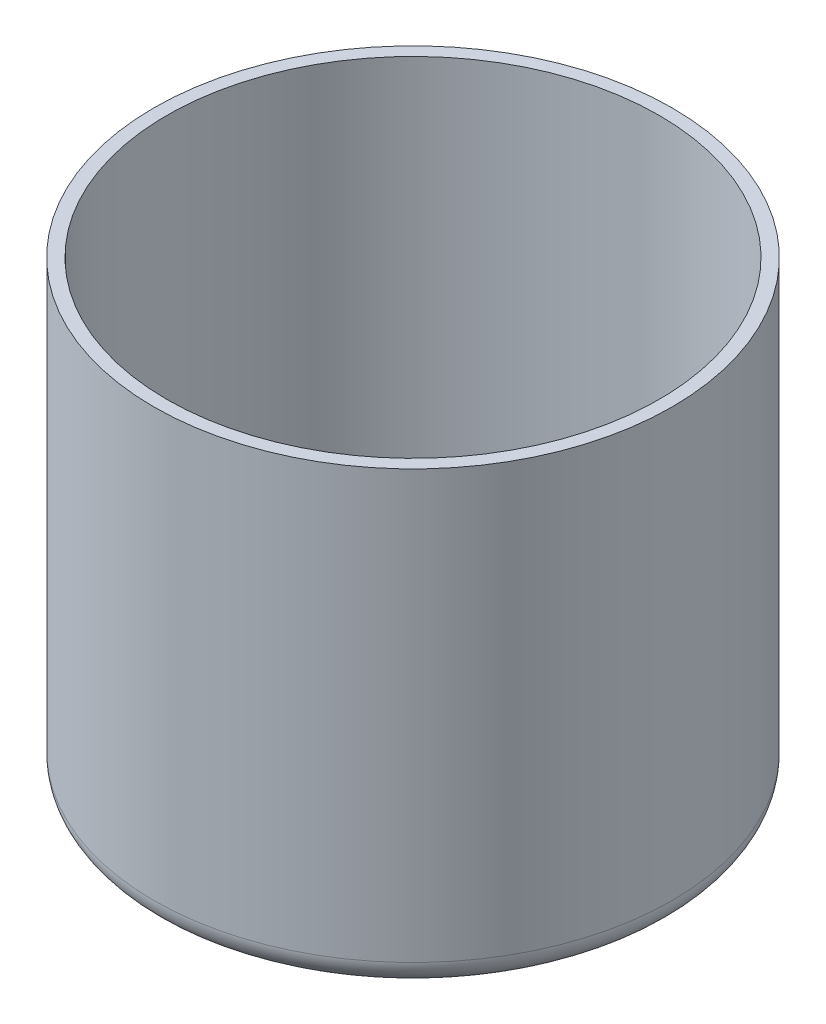
SolidWorks part; units mm, degrees
ref_plane "Front Plane" through (0, 0, 0) normal (0, 0, 1) x (1, 0, 0)
ref_plane "Top Plane" through (0, 0, 0) normal (0, 1, 0) x (1, 0, 0)
ref_plane "Right Plane" through (0, 0, 0) normal (1, 0, 0) x (0, 0, -1)
sketch "Sketch1" plane through (0, 0, 0) normal (0, 0, 1) x (1, 0, 0)
  line L0 (0, 0) -> (0, 28.1093) construction
  line L1 (-20, 2.4232) -> (-20, -32.5768)
  line L2 (-20, -32.5768) -> (0, -32.5768)
  line L4 (-19, 2.4232) -> (-19, -31.5768)
  line L5 (-19, -31.5768) -> (0, -31.5768)
  line L6 (-20, 2.4232) -> (-19, 2.4232)
  line L9 (0, -31.5768) -> (0, -32.5768)
  dimension "D2" = 20
  dimension "D3" = 0
  dimension "D4" = 35
  dimension "D5" = 32.5768
  dimension "D1" = 1
revolve "Revolve1" add sketch "Sketch1" angle 360 about L0
fillet "Fillet1" radius 2 1 edges at (0, -32.5768, -20)
